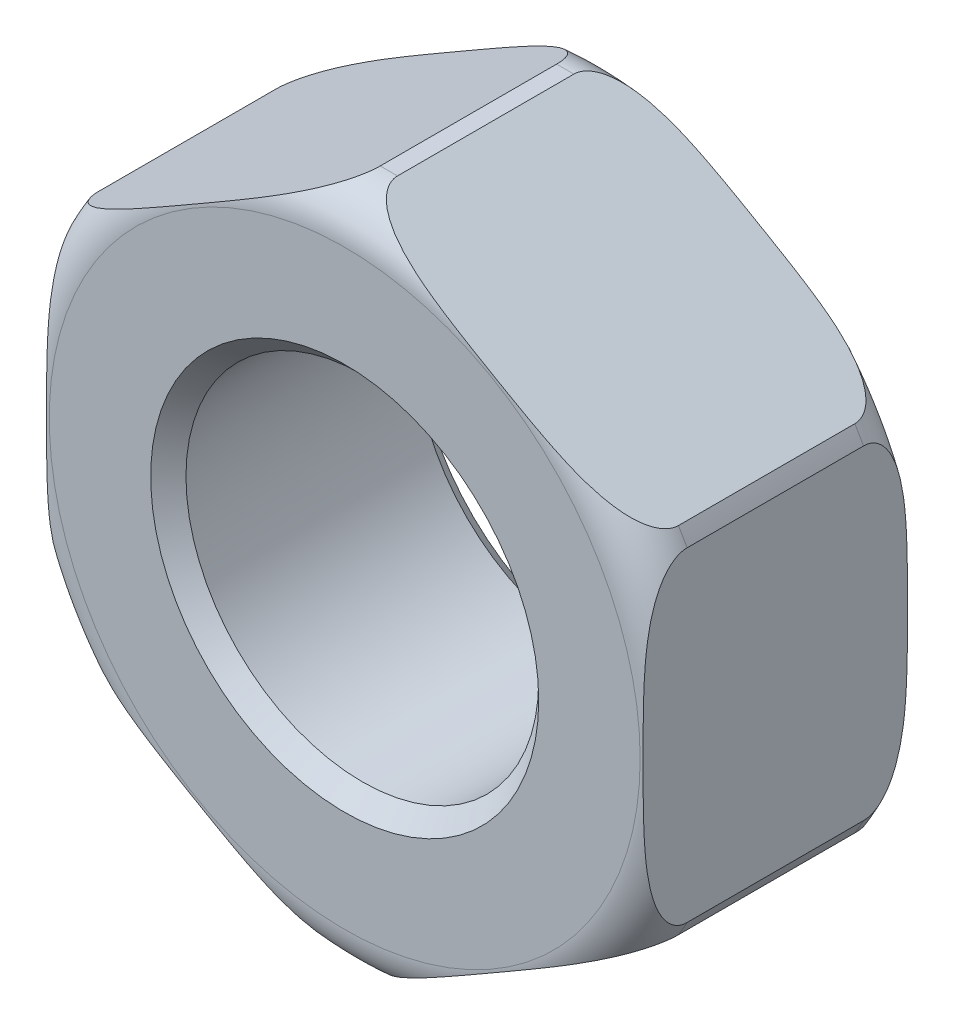
SolidWorks part; units mm, degrees
ref_plane "Plan de face" through (0, 0, 0) normal (0, 0, 1) x (1, 0, 0)
ref_plane "Plan de dessus" through (0, 0, 0) normal (0, 1, 0) x (1, 0, 0)
ref_plane "Plan de droite" through (0, 0, 0) normal (1, 0, 0) x (0, 0, -1)
sketch "Esquisse1" plane through (0, 0, 0) normal (0, 0, 1) x (1, 0, 0)
  circle A0 centre (0, 0) radius 3.85
  circle A1 centre (0, 0) radius 2
extrude "Extrusion1" add sketch "Esquisse1" along normal blind 3
fillet "Congé1" radius 0.5 2 edges at (3.85, 0, 0) (3.85, 0, 3)
sketch "Esquisse2" plane through (0, 0, 3) normal (0, 0, 1) x (1, 0, 0)
  line L3 (3.3821, 1.9527) -> (0, 3.9053)
  line L4 (0, 3.9053) -> (-3.3821, 1.9527)
  line L5 (-3.3821, 1.9527) -> (-3.3821, -1.9527)
  line L6 (-3.3821, -1.9527) -> (0, -3.9053)
  line L7 (0, -3.9053) -> (3.3821, -1.9527)
  line L8 (3.3821, -1.9527) -> (3.3821, 1.9527)
extrude "Enlèv. mat.-Extru.1" cut sketch "Esquisse2" against normal blind 3 flip side to cut
chamfer "Chanfrein1" distance 0.2 angle 45 2 edges at (2, 0, 0) (2, 0, 3)
